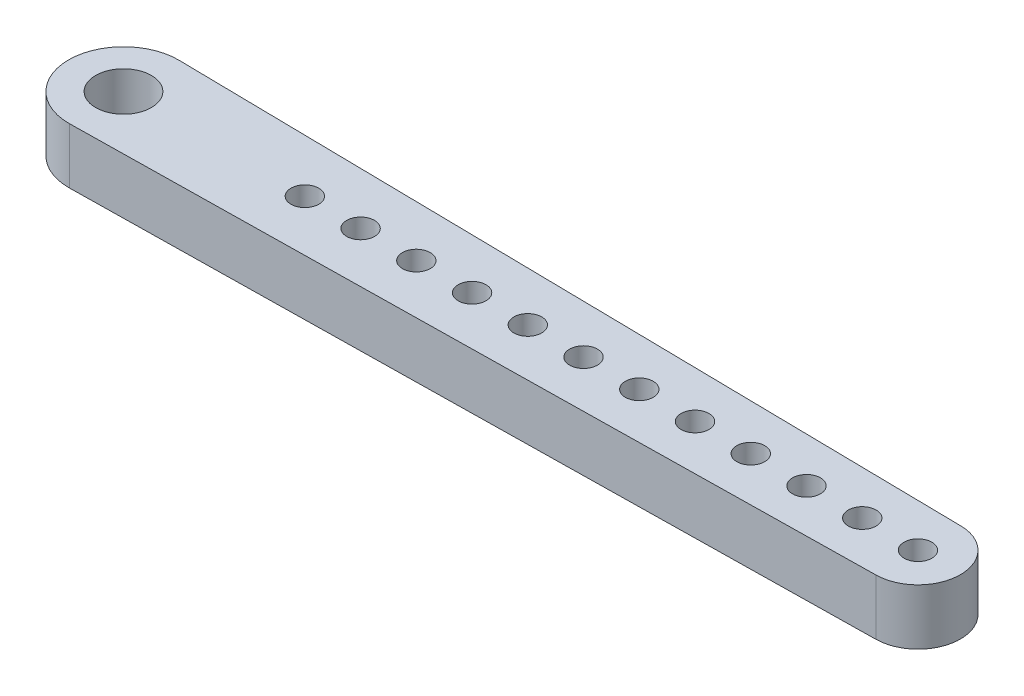
SolidWorks part; units mm, degrees
ref_plane "Front Plane" through (0, 0, 0) normal (0, 0, 1) x (1, 0, 0)
ref_plane "Top Plane" through (0, 0, 0) normal (0, 1, 0) x (1, 0, 0)
ref_plane "Right Plane" through (0, 0, 0) normal (1, 0, 0) x (0, 0, -1)
sketch "Sketch2" plane through (0, 0, 0) normal (0, 1, 0) x (1, 0, 0)
  line L0 (0, 0) -> (0, 6.35)
  line L1 (0, 6.35) -> (101.6, 4.7625)
  line L2 (101.6, 4.7625) -> (101.6, 0)
  line L3 (101.6, 0) -> (0, 0)
  line L4 (0, 0) -> (-147.5242, 0) construction
  dimension "D1" = 12.7
  dimension "D2" = 9.525
  dimension "D3" = 101.6
extrude "Boss-Extrude1" add sketch "Sketch2" along normal blind 6.35
mirror "Mirror1" about plane through (101.6, 6.35, 0) normal (0, 0, -1) of "Boss-Extrude1"
fillet "Fillet1" radius 4.8375 4 edges at (101.6, 3.175, 4.7625) (101.6, 0, 0) (101.6, 6.35, 0) (101.6, 3.175, -4.7625)
fillet "Fillet3" radius 6.2516 4 edges at (0, 6.35, 0) (0, 3.175, 6.35) (0, 0, 0) (0, 3.175, -6.35)
sketch "Sketch3" plane through (0, 6.35, 0) normal (0, 1, 0) x (1, 0, 0)
  line L0 (6.2516, 0) -> (96.7625, 0) construction
  circle A0 centre (6.2516, 0) radius 3.175
  circle A1 centre (96.7625, 0) radius 1.5875
  dimension "D1" = 6.35
  dimension "D2" = 3.175
extrude "Cut-Extrude1" cut sketch "Sketch3" against normal through all
sketch "Sketch4" plane through (0, 6.35, 0) normal (0, 1, 0) x (1, 0, 0)
  line L0 (6.2516, 0) -> (96.7625, 0) construction
sketch "Sketch5" plane through (0, 6.35, 0) normal (0, 1, 0) x (1, 0, 0)
  circle A0 centre (90.4125, 0) radius 1.5875
  circle A1 centre (96.7625, 0) radius 1.5875 construction
  dimension "D1" = 6.35
extrude "Cut-Extrude2" cut sketch "Sketch5" against normal through all
pattern_linear "LPattern1" count 11 spacing 6.35 along (-1, 0, 0) of "Cut-Extrude2"
